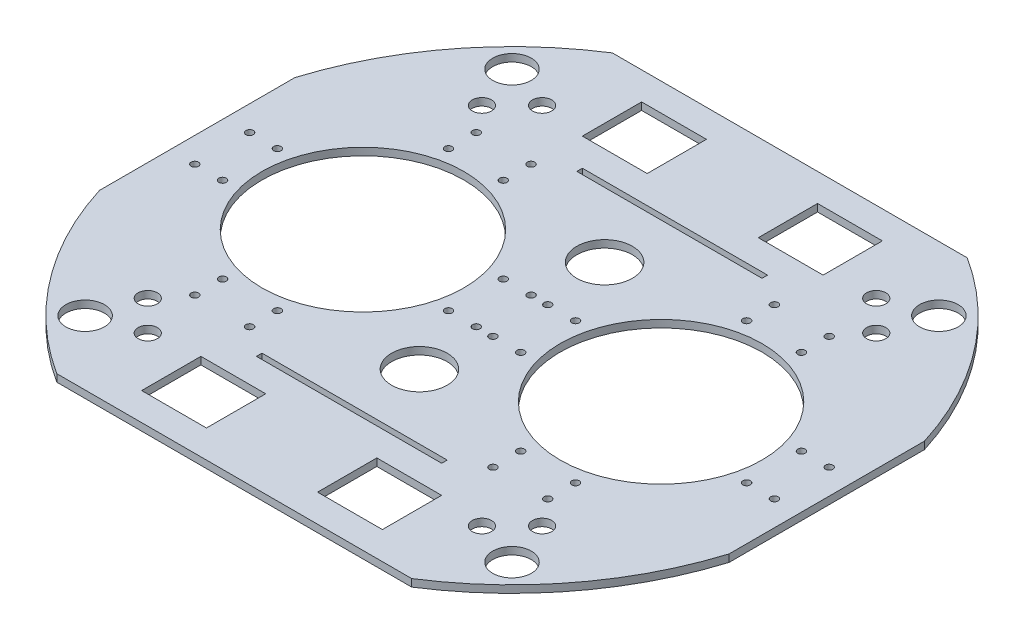
SolidWorks part; units mm, degrees
material "Hexcel AS4C (3000 丝)"
ref_plane "Front" through (0, 0, 0) normal (0, 0, 1) x (1, 0, 0)
ref_plane "Top" through (0, 0, 0) normal (0, 1, 0) x (1, 0, 0)
ref_plane "Right" through (0, 0, 0) normal (1, 0, 0) x (0, 0, -1)
sketch "草图1" plane through (0, 0, 0) normal (0, 1, 0) x (1, 0, 0)
  line L0 (0, 0) -> (20, 0) construction
  line L1 (20, 0) -> (129, 0) construction
  line L2 (0, 0) -> (0, 43.8486) construction
  line L3 (-129, 0) -> (-178, 0) construction
  circle A7 centre (0, 0) radius 178
  point P33 (0, 0)
extrude "凸台-拉伸1" add sketch "草图1" along normal blind 4
sketch "草图2" plane through (0, 4, 0) normal (0, 1, 0) x (1, 0, 0)
  line L0 (0, 0) -> (-125.865, -125.865) construction
  line L1 (125.865, 125.865) -> (115.2584, 115.2584) construction
  line L2 (-125.865, -125.865) -> (-95.8738, -95.8738) construction
  line L3 (-95.8738, -95.8738) -> (-90.2169, -101.5306) construction
  line L5 (-90.2169, -101.5306) -> (-95.1667, -106.4804) construction
  line L6 (-95.1667, -106.4804) -> (-90.2169, -111.4301) construction
  line L7 (-90.2169, -111.4301) -> (-85.2672, -106.4804) construction
  line L8 (-85.2672, -106.4804) -> (-90.2169, -101.5306) construction
  line L9 (-90.2169, -101.5306) -> (-90.2169, -111.4301) construction
  line L20 (-90.2169, -111.4301) -> (-90.2169, -106.4804) construction
  line L21 (-90.2169, -106.4804) -> (-85.2672, -106.4804) construction
  line L29 (0, 0) -> (-125.865, 125.865) construction
  line L38 (0, 0) -> (125.865, 125.865) construction
  line L47 (0, 0) -> (125.865, -125.865) construction
  circle A6 centre (0, 0) radius 178 construction
  circle A7 centre (115.2584, 115.2584) radius 10.414
  circle A9 centre (-90.2169, -106.4804) radius 5.2
  circle A10 centre (-106.4804, -90.2169) radius 5.2
  circle A11 centre (115.2584, -115.2584) radius 10.414
  circle A12 centre (-115.2584, -115.2584) radius 10.414
  circle A13 centre (-115.2584, 115.2584) radius 10.414
  circle A14 centre (-90.2169, 106.4804) radius 5.2
  circle A15 centre (-106.4804, 90.2169) radius 5.2
  circle A16 centre (106.4804, 90.2169) radius 5.2
  circle A17 centre (90.2169, 106.4804) radius 5.2
  circle A18 centre (90.2169, -106.4804) radius 5.2
  circle A19 centre (106.4804, -90.2169) radius 5.2
  point P27 (0, 0)
  point P43 (0, 0)
  dimension "D1" = 4
  dimension "D2" = 4
extrude "切除-拉伸1" cut sketch "草图2" against normal blind 10
sketch "草图4" plane through (0, 0, 0) normal (0, -1, 0) x (1, 0, 0)
  circle A1 centre (80.5, 0) radius 54.5
  circle A3 centre (-80.5, 0) radius 54.5
  point P3 (0, 0)
  point P4 (0, 0)
extrude "切除-拉伸2" cut sketch "草图4" against normal blind 10
sketch "草图5" plane through (0, 4, 0) normal (0, 1, 0) x (1, 0, 0)
  line L0 (0, 0) -> (-24, 0) construction
  line L1 (-24, 0) -> (-24, 20) construction
  line L2 (-24, 0) -> (-24, -20) construction
  line L3 (-12, 0) -> (-12, -14.8) construction
  line L4 (-12, -14.8) -> (-19.5, -14.8) construction
  line L5 (-12, -14.8) -> (-4.5, -14.8) construction
  line L6 (0, 0) -> (0, 20) construction
  line L7 (-24, 0) -> (-26, 0) construction
  circle A82 centre (-19.5, -14.8) radius 2
  circle A83 centre (-4.5, -14.8) radius 2
  circle A84 centre (-4.5, 14.8) radius 2
  circle A85 centre (-19.5, 14.8) radius 2
  circle A86 centre (-80.5, 0) radius 54.5 construction
  circle A87 centre (4.5, -14.8) radius 2
  circle A88 centre (19.5, -14.8) radius 2
  circle A89 centre (19.5, 14.8) radius 2
  circle A90 centre (4.5, 14.8) radius 2
  circle A91 centre (-65.7, -61) radius 2
  circle A92 centre (-65.7, -76) radius 2
  circle A93 centre (-95.3, -61) radius 2
  circle A94 centre (-95.3, -76) radius 2
  circle A95 centre (-141.5, -14.8) radius 2
  circle A96 centre (-156.5, -14.8) radius 2
  circle A97 centre (-141.5, 14.8) radius 2
  circle A98 centre (-156.5, 14.8) radius 2
  circle A99 centre (-95.3, 61) radius 2
  circle A100 centre (-95.3, 76) radius 2
  circle A101 centre (-65.7, 61) radius 2
  circle A102 centre (-65.7, 76) radius 2
  circle A103 centre (95.3, 76) radius 2
  circle A104 centre (95.3, 61) radius 2
  circle A105 centre (65.7, 76) radius 2
  circle A106 centre (65.7, 61) radius 2
  circle A107 centre (156.5, -14.8) radius 2
  circle A108 centre (141.5, -14.8) radius 2
  circle A109 centre (156.5, 14.8) radius 2
  circle A110 centre (141.5, 14.8) radius 2
  circle A111 centre (65.7, -76) radius 2
  circle A112 centre (65.7, -61) radius 2
  circle A113 centre (95.3, -76) radius 2
  circle A114 centre (95.3, -61) radius 2
  point P53 (-80.5, 0)
  point P78 (80.5, 0)
extrude "切除-拉伸3" cut sketch "草图5" against normal blind 10
sketch "草图8" plane through (0, 0, 0) normal (0, -1, 0) x (1, 0, 0)
  line L0 (0, 0) -> (170, 0) construction
  line L1 (170, 0) -> (170, 52.7636) construction
  line L2 (0, 0) -> (0, 150) construction
  line L3 (0, 150) -> (95.8332, 150) construction
  line L4 (95.8332, 150) -> (0, 150)
  line L5 (0, 150) -> (-95.8332, 150)
  line L6 (170, 52.7636) -> (170, 0)
  line L7 (170, 0) -> (170, -52.7636)
  line L8 (0, -150) -> (-95.8332, -150)
  line L9 (95.8332, -150) -> (0, -150)
  line L10 (-170, 0) -> (-170, -52.7636)
  line L11 (-170, 52.7636) -> (-170, 0)
  circle A0 centre (0, 0) radius 178 construction
  arc A1 (-170, 52.7636) -> (-170, -52.7636) centre (0, 0) ccw
  arc A2 (95.8332, 150) -> (-95.8332, 150) centre (0, 0) ccw
  arc A3 (170, -52.7636) -> (170, 52.7636) centre (0, 0) ccw
  arc A4 (-95.8332, -150) -> (95.8332, -150) centre (0, 0) ccw
extrude "切除-拉伸4" cut sketch "草图8" against normal blind 10
sketch "草图11" plane through (0, 0, 0) normal (0, -1, 0) x (1, 0, 0)
  line L0 (0, -150) -> (0, -85) construction
  line L1 (95.8332, -150) -> (-95.8332, -150) construction
  line L2 (0, -85) -> (50, -85) construction
  line L3 (50, -85) -> (50, -88) construction
  line L4 (-50, -85) -> (50, -85)
  line L5 (50, -85) -> (50, -88)
  line L6 (50, -88) -> (-50, -88)
  line L7 (-50, -85) -> (-50, -88)
  line L8 (0, 0) -> (80.5, 0) construction
  line L9 (0, -150) -> (80, -150) construction
  line L10 (80, -150) -> (80, -135) construction
  line L11 (65, -135) -> (30, -135)
  line L12 (50, -88) -> (50, -103) construction
  line L13 (50, -103) -> (80, -103) construction
  line L15 (65, -103) -> (30, -103)
  line L17 (-80, -119) -> (-65, -119) construction
  line L18 (-65, -119) -> (-65, -103)
  line L19 (-65, -119) -> (-65, -135)
  line L20 (80, -119) -> (65, -119) construction
  line L21 (-50, 85) -> (-50, 88)
  line L22 (65, -103) -> (65, -135)
  line L23 (50, 85) -> (50, 88)
  line L24 (50, 88) -> (-50, 88)
  line L25 (-50, 85) -> (50, 85)
  line L31 (0, -135) -> (0, -103) construction
  line L32 (0, -103) -> (0, -119) construction
  line L33 (0, -119) -> (30, -119) construction
  line L34 (30, -119) -> (30, -103)
  line L35 (30, -119) -> (30, -135)
  line L36 (-30, -119) -> (-30, -135)
  line L37 (-30, -119) -> (-30, -103)
  line L38 (-30, -103) -> (-65, -103)
  line L39 (-30, -135) -> (-65, -135)
  line L40 (-65, 119) -> (-65, 103)
  line L41 (-30, 103) -> (-65, 103)
  line L42 (-30, 119) -> (-30, 103)
  line L43 (-30, 119) -> (-30, 135)
  line L44 (-30, 135) -> (-65, 135)
  line L45 (-65, 119) -> (-65, 135)
  line L46 (65, 103) -> (65, 135)
  line L47 (65, 103) -> (30, 103)
  line L48 (30, 119) -> (30, 103)
  line L49 (30, 119) -> (30, 135)
  line L50 (65, 135) -> (30, 135)
  point P10 (0, -88)
extrude "切除-拉伸5" cut sketch "草图11" against normal blind 10
sketch "草图13" plane through (0, 0, 0) normal (0, -1, 0) x (1, 0, 0)
  line L0 (0, 0) -> (0, -50) construction
  line L1 (0, 0) -> (26, 0) construction
  circle A0 centre (0, -50) radius 15
  circle A1 centre (80.5, 0) radius 54.5 construction
  circle A2 centre (0, 50) radius 15
extrude "切除-拉伸6" cut sketch "草图13" against normal blind 10
sketch "草图14" plane through (0, 4, 0) normal (0, 1, 0) x (1, 0, 0)
  line L0 (0, 0) -> (80.5, 0)
